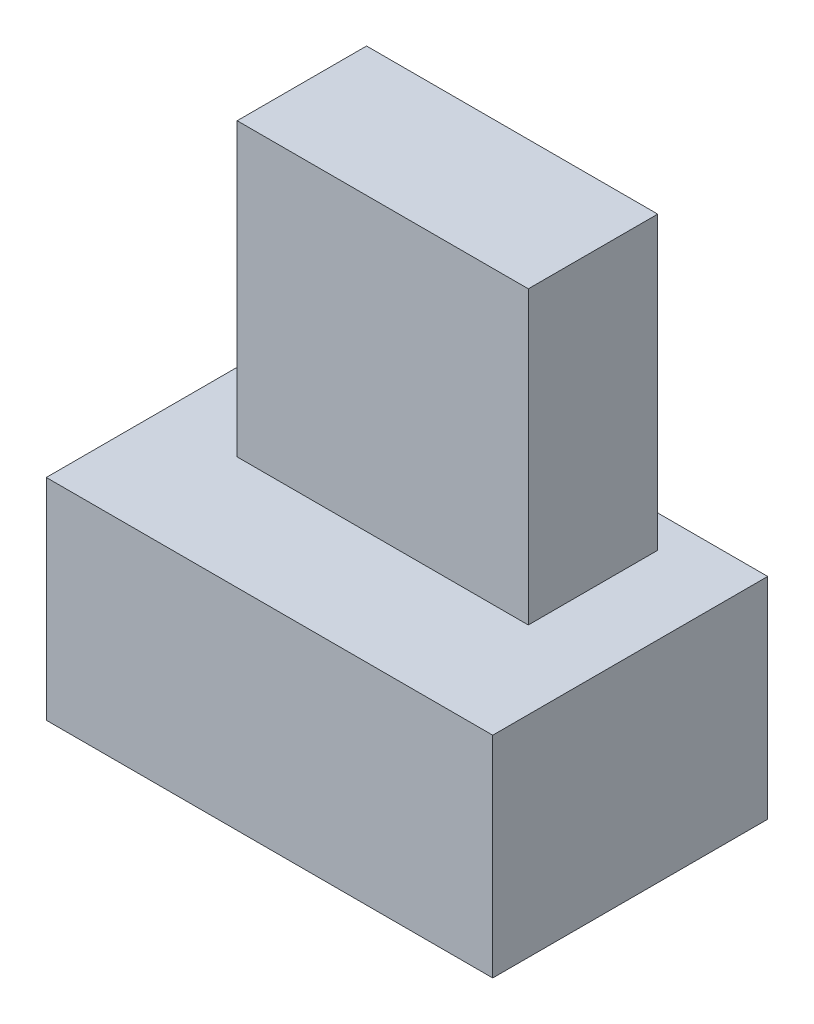
SolidWorks part; units mm, degrees
ref_plane "Front Plane" through (0, 0, 0) normal (0, 0, 1) x (1, 0, 0)
ref_plane "Top Plane" through (0, 0, 0) normal (0, 1, 0) x (1, 0, 0)
ref_plane "Right Plane" through (0, 0, 0) normal (1, 0, 0) x (0, 0, -1)
sketch "Sketch2" plane through (0, 0, 0) normal (0, 1, 0) x (1, 0, 0)
  line L1 (0, 0) -> (13.8, 0)
  line L2 (0, 0) -> (0, 8.5)
  line L3 (0, 8.5) -> (13.8, 8.5)
  line L4 (13.8, 0) -> (13.8, 8.5)
extrude "Boss-Extrude1" add sketch "Sketch2" along normal blind 6.5
sketch "Sketch5" plane through (0, 6.5, 0) normal (0, 1, 0) x (-1, 0, 0)
  line L1 (-2.4, -3.5) -> (-11.4, -3.5)
  line L2 (-2.4, -3.5) -> (-2.4, -7.5)
  line L3 (-2.4, -7.5) -> (-11.4, -7.5)
  line L4 (-11.4, -3.5) -> (-11.4, -7.5)
extrude "Boss-Extrude3" add sketch "Sketch5" along normal blind 9
